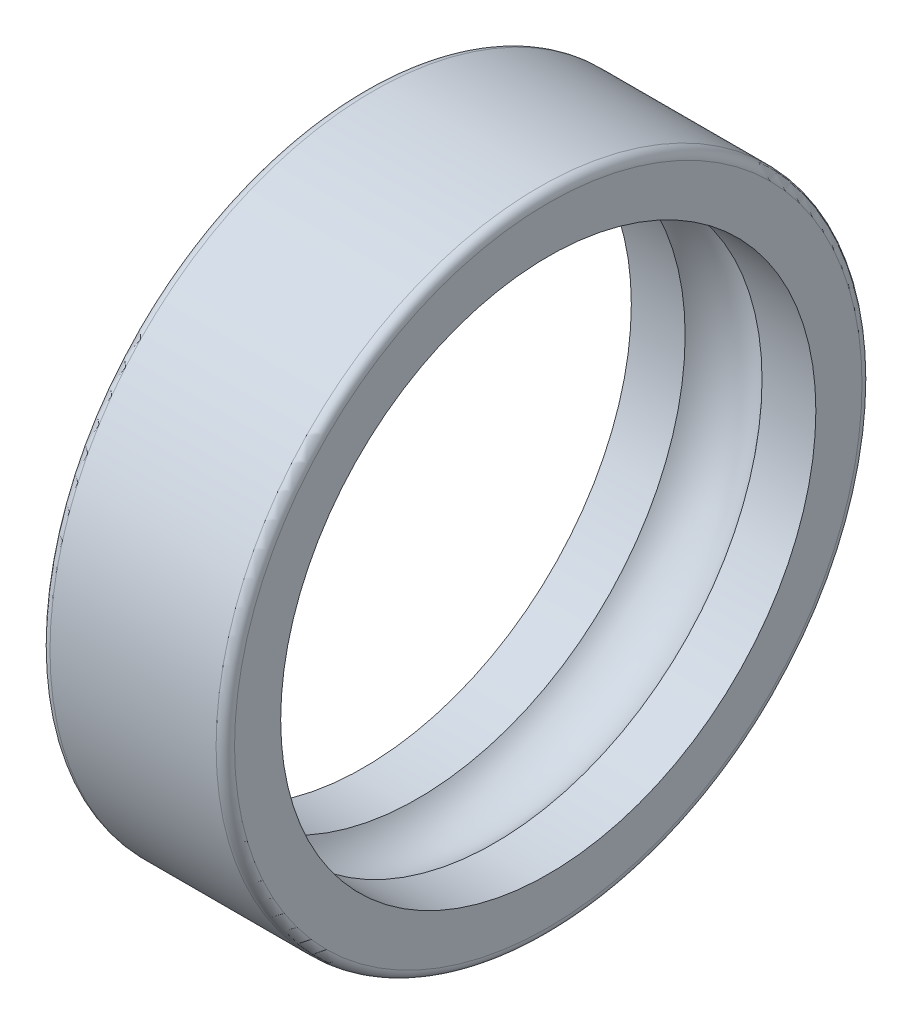
SolidWorks part; units mm, degrees
ref_plane "Front Plane" through (0, 0, 0) normal (0, 0, 1) x (1, 0, 0)
ref_plane "Top Plane" through (0, 0, 0) normal (0, 1, 0) x (1, 0, 0)
ref_plane "Right Plane" through (0, 0, 0) normal (1, 0, 0) x (0, 0, -1)
sketch "Sketch1" plane through (0, 0, 0) normal (0, 0, 1) x (1, 0, 0)
  line L0 (2.5, 5.4) -> (6, 5.4)
  line L1 (6, -12) -> (-6, -12)
  line L2 (6, 5.4) -> (6, 9)
  line L3 (6, 9) -> (-6, 9)
  line L4 (-6, 5.4) -> (-6, 9)
  line L7 (-6, -12) -> (6, -12)
  line L9 (-6, 5.4) -> (-2.5, 5.4)
  arc A0 (2.5, 5.4) -> (-2.5, 5.4) centre (0, 3.4025) ccw
  point P0 (0, 0)
  point P8 (0, 0)
  dimension "D5" = 6.4
  dimension "D1" = 12
  dimension "D2" = 21
  dimension "D3" = 17.4
revolve "Revolve1" add sketch "Sketch1" angle 360 about L1
fillet "Fillet1" radius 0.6 2 edges at (-6, -12, -21) (6, -12, -21)
